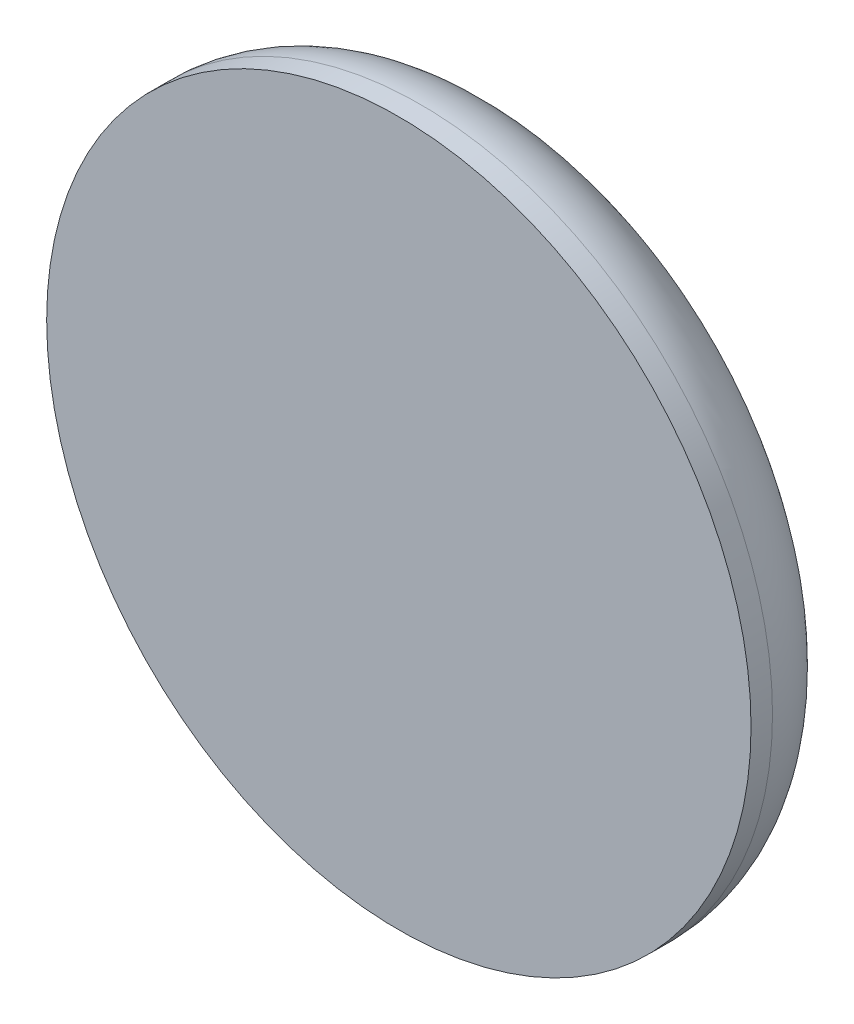
SolidWorks part; units mm, degrees
ref_plane "Front Plane" through (0, 0, 0) normal (0, 0, 1) x (1, 0, 0)
ref_plane "Top Plane" through (0, 0, 0) normal (0, 1, 0) x (1, 0, 0)
ref_plane "Right Plane" through (0, 0, 0) normal (1, 0, 0) x (0, 0, -1)
sketch "Croquis1" plane through (0, 0, 0) normal (0, 1, 0) x (1, 0, 0)
  line L0 (0, 0) -> (0.625, 0)
  line L1 (0, 0) -> (0, 0.25)
  line L2 (0.625, 0) -> (0.625, 0.0381)
  arc A0 (0, 0.25) -> (0.5134, 0.1831) centre (0, -1.7531) cw
  arc A1 (0.625, 0.0381) -> (0.5134, 0.1831) centre (0.475, 0.0381) ccw
  point P8 (0.625, 0.15)
  dimension "D4" = 0.15
  dimension "D1" = 0.25
  dimension "D2" = 0.625
  dimension "D3" = 0.15
revolve "Revolución1" add sketch "Croquis1" angle 360 about L1
